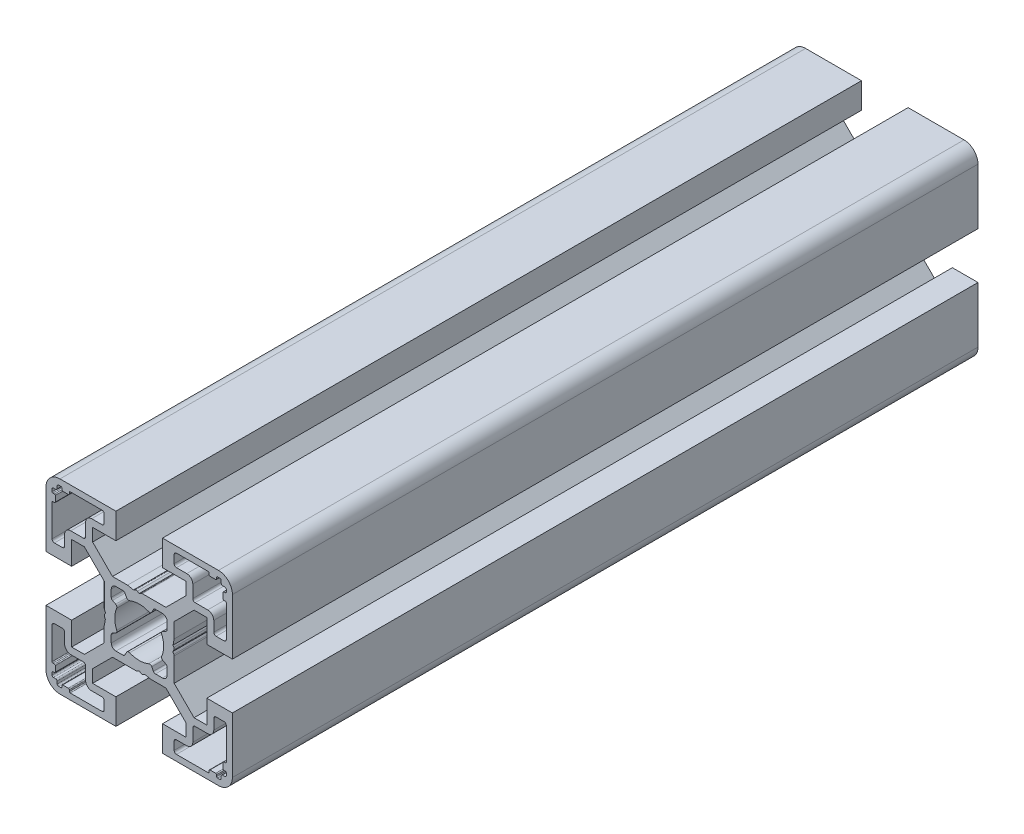
SolidWorks part; units mm, degrees
ref_plane "Front Plane" through (0, 0, 0) normal (0, 0, 1) x (1, 0, 0)
ref_plane "Top Plane" through (0, 0, 0) normal (0, 1, 0) x (1, 0, 0)
ref_plane "Right Plane" through (0, 0, 0) normal (1, 0, 0) x (0, 0, -1)
sketch "Sketch1" plane through (0, 0, 0) normal (0, 0, 1) x (1, 0, 0)
  line L0 (-11.7678, -10) -> (-14.5, -10)
  line L1 (-14.5, -10) -> (-14.5, -5)
  line L2 (-14.5, -5) -> (-20, -5)
  line L3 (-20, -5) -> (-20, -17)
  line L4 (-17, -20) -> (-5, -20)
  line L5 (-5, -20) -> (-5, -14.5)
  line L6 (-5, -14.5) -> (-10, -14.5)
  line L7 (-10, -14.5) -> (-10, -11.7678)
  line L8 (-10, -11.7678) -> (-5.7322, -7.5)
  line L9 (-5.7322, -7.5) -> (-0.6536, -7.5)
  line L10 (-0.4036, -7.433) -> (0, -7.2)
  line L11 (0, -7.2) -> (0.4036, -7.433)
  line L12 (0.9036, -7.433) -> (1.2189, -7.251)
  line L13 (1.2189, -7.251) -> (2.5, -7.5)
  line L14 (2.5, -7.5) -> (5.7322, -7.5)
  line L15 (5.7322, -7.5) -> (10, -11.7678)
  line L16 (10, -11.7678) -> (10, -14.5)
  line L17 (10, -14.5) -> (5, -14.5)
  line L18 (5, -14.5) -> (5, -20)
  line L19 (5, -20) -> (17, -20)
  line L20 (20, -17) -> (20, -5)
  line L21 (20, -5) -> (14.5, -5)
  line L22 (14.5, -5) -> (14.5, -10)
  line L23 (14.5, -10) -> (11.7678, -10)
  line L24 (11.7678, -10) -> (7.5, -5.7322)
  line L25 (7.5, -5.7322) -> (7.5, -0.6536)
  line L26 (7.433, -0.4036) -> (7.2, 0)
  line L27 (7.2, 0) -> (7.433, 0.4036)
  line L28 (7.433, 0.9036) -> (7.251, 1.2189)
  line L29 (7.251, 1.2189) -> (7.5, 2.5)
  line L30 (7.5, 2.5) -> (7.5, 5.7322)
  line L31 (7.5, 5.7322) -> (11.7678, 10)
  line L32 (11.7678, 10) -> (14.5, 10)
  line L33 (14.5, 10) -> (14.5, 5)
  line L34 (14.5, 5) -> (20, 5)
  line L35 (20, 5) -> (20, 17)
  line L36 (17, 20) -> (5, 20)
  line L37 (5, 20) -> (5, 14.5)
  line L38 (5, 14.5) -> (10, 14.5)
  line L39 (10, 14.5) -> (10, 11.7678)
  line L40 (10, 11.7678) -> (5.7322, 7.5)
  line L41 (5.7322, 7.5) -> (0.6536, 7.5)
  line L42 (0.4036, 7.433) -> (0, 7.2)
  line L43 (0, 7.2) -> (-0.4036, 7.433)
  line L44 (-0.9036, 7.433) -> (-1.2189, 7.251)
  line L45 (-1.2189, 7.251) -> (-2.5, 7.5)
  line L46 (-2.5, 7.5) -> (-5.7322, 7.5)
  line L47 (-5.7322, 7.5) -> (-10, 11.7678)
  line L48 (-10, 11.7678) -> (-10, 14.5)
  line L49 (-10, 14.5) -> (-5, 14.5)
  line L50 (-5, 14.5) -> (-5, 20)
  line L51 (-5, 20) -> (-17, 20)
  line L52 (-20, 17) -> (-20, 5)
  line L53 (-20, 5) -> (-14.5, 5)
  line L54 (-14.5, 5) -> (-14.5, 10)
  line L55 (-14.5, 10) -> (-11.7678, 10)
  line L56 (-11.7678, 10) -> (-7.5, 5.7322)
  line L57 (-7.5, 5.7322) -> (-7.5, 0.6536)
  line L58 (-7.433, 0.4036) -> (-7.2, 0)
  line L59 (-7.2, 0) -> (-7.433, -0.4036)
  line L60 (-7.433, -0.9036) -> (-7.251, -1.2189)
  line L61 (-7.251, -1.2189) -> (-7.5, -2.5)
  line L62 (-7.5, -2.5) -> (-7.5, -5.7322)
  line L63 (-7.5, -5.7322) -> (-11.7678, -10)
  line L64 (7.5, 16.5) -> (7.5, 18.2)
  line L65 (8, 18.7) -> (14.8, 18.7)
  line L66 (15, 18.5) -> (15, 18.2)
  line L67 (15.2, 18) -> (16.4, 18)
  line L68 (16.6, 18.2) -> (16.6, 18.5)
  line L69 (16.8, 18.7) -> (17.3, 18.7)
  line L70 (17.6, 18.4) -> (17.6, 17.9)
  line L71 (17.9, 17.6) -> (18.4, 17.6)
  line L72 (18.7, 17.3) -> (18.7, 16.8)
  line L73 (18.5, 16.6) -> (18.2, 16.6)
  line L74 (18, 16.4) -> (18, 15.2)
  line L75 (18.2, 15) -> (18.5, 15)
  line L76 (18.7, 14.8) -> (18.7, 8)
  line L77 (18.2, 7.5) -> (16.5, 7.5)
  line L78 (16, 8) -> (16, 10.2)
  line L79 (14.7, 11.5) -> (12, 11.5)
  line L80 (11.5, 12) -> (11.5, 14.7)
  line L81 (10.2, 16) -> (8, 16)
  line L82 (14.8, -18.7) -> (8, -18.7)
  line L83 (7.5, -18.2) -> (7.5, -16.5)
  line L84 (8, -16) -> (10.2, -16)
  line L85 (11.5, -14.7) -> (11.5, -12)
  line L86 (12, -11.5) -> (14.7, -11.5)
  line L87 (16, -10.2) -> (16, -8)
  line L88 (16.5, -7.5) -> (18.2, -7.5)
  line L89 (18.7, -8) -> (18.7, -14.8)
  line L90 (18.5, -15) -> (18.2, -15)
  line L91 (18, -15.2) -> (18, -16.4)
  line L92 (18.2, -16.6) -> (18.5, -16.6)
  line L93 (18.7, -16.8) -> (18.7, -17.3)
  line L94 (18.4, -17.6) -> (17.9, -17.6)
  line L95 (17.6, -17.9) -> (17.6, -18.4)
  line L96 (17.3, -18.7) -> (16.8, -18.7)
  line L97 (16.6, -18.5) -> (16.6, -18.2)
  line L98 (16.4, -18) -> (15.2, -18)
  line L99 (15, -18.2) -> (15, -18.5)
  line L100 (-18.7, 16.8) -> (-18.7, 17.3)
  line L101 (-18.4, 17.6) -> (-17.9, 17.6)
  line L102 (-17.6, 17.9) -> (-17.6, 18.4)
  line L103 (-17.3, 18.7) -> (-16.8, 18.7)
  line L104 (-16.6, 18.5) -> (-16.6, 18.2)
  line L105 (-16.4, 18) -> (-15.2, 18)
  line L106 (-15, 18.2) -> (-15, 18.5)
  line L107 (-14.8, 18.7) -> (-8, 18.7)
  line L108 (-7.5, 18.2) -> (-7.5, 16.5)
  line L109 (-8, 16) -> (-10.2, 16)
  line L110 (-11.5, 14.7) -> (-11.5, 12)
  line L111 (-12, 11.5) -> (-14.7, 11.5)
  line L112 (-16, 10.2) -> (-16, 8)
  line L113 (-16.5, 7.5) -> (-18.2, 7.5)
  line L114 (-18.7, 8) -> (-18.7, 14.8)
  line L115 (-18.5, 15) -> (-18.2, 15)
  line L116 (-18, 15.2) -> (-18, 16.4)
  line L117 (-18.2, 16.6) -> (-18.5, 16.6)
  line L118 (-18.7, -14.8) -> (-18.7, -8)
  line L119 (-18.2, -7.5) -> (-16.5, -7.5)
  line L120 (-16, -8) -> (-16, -10.2)
  line L121 (-14.7, -11.5) -> (-12, -11.5)
  line L122 (-11.5, -12) -> (-11.5, -14.7)
  line L123 (-10.2, -16) -> (-8, -16)
  line L124 (-7.5, -16.5) -> (-7.5, -18.2)
  line L125 (-8, -18.7) -> (-14.8, -18.7)
  line L126 (-15, -18.5) -> (-15, -18.2)
  line L127 (-15.2, -18) -> (-16.4, -18)
  line L128 (-16.6, -18.2) -> (-16.6, -18.5)
  line L129 (-16.8, -18.7) -> (-17.3, -18.7)
  line L130 (-17.6, -18.4) -> (-17.6, -17.9)
  line L131 (-17.9, -17.6) -> (-18.4, -17.6)
  line L132 (-18.7, -17.3) -> (-18.7, -16.8)
  line L133 (-18.5, -16.6) -> (-18.2, -16.6)
  line L134 (-18, -16.4) -> (-18, -15.2)
  line L135 (-18.2, -15) -> (-18.5, -15)
  line L136 (-6, 3.4907) -> (-6, 5)
  line L137 (-5, 6) -> (-3.4907, 6)
  line L138 (-3.0492, 5.7347) -> (-2.6892, 5.0577)
  line L139 (2.6892, 5.0577) -> (3.0492, 5.7347)
  line L140 (3.4907, 6) -> (5, 6)
  line L141 (6, 5) -> (6, 3.4907)
  line L142 (5.7347, 3.0492) -> (5.0577, 2.6892)
  line L143 (5.0577, -2.6892) -> (5.7347, -3.0492)
  line L144 (6, -3.4907) -> (6, -5)
  line L145 (5, -6) -> (3.4907, -6)
  line L146 (3.0492, -5.7347) -> (2.6892, -5.0577)
  line L147 (-2.6892, -5.0577) -> (-3.0492, -5.7347)
  line L148 (-3.4907, -6) -> (-5, -6)
  line L149 (-6, -5) -> (-6, -3.4907)
  line L150 (-5.7347, -3.0492) -> (-5.0577, -2.6892)
  line L151 (-5.0577, 2.6892) -> (-5.7347, 3.0492)
  arc A0 (-20, -17) -> (-17, -20) centre (-17, -17) ccw
  arc A1 (-0.6536, -7.5) -> (-0.4036, -7.433) centre (-0.6536, -7) ccw
  arc A2 (0.4036, -7.433) -> (0.9036, -7.433) centre (0.6536, -7) ccw
  arc A3 (17, -20) -> (20, -17) centre (17, -17) ccw
  arc A4 (7.5, -0.6536) -> (7.433, -0.4036) centre (7, -0.6536) ccw
  arc A5 (7.433, 0.4036) -> (7.433, 0.9036) centre (7, 0.6536) ccw
  arc A6 (20, 17) -> (17, 20) centre (17, 17) ccw
  arc A7 (0.6536, 7.5) -> (0.4036, 7.433) centre (0.6536, 7) ccw
  arc A8 (-0.4036, 7.433) -> (-0.9036, 7.433) centre (-0.6536, 7) ccw
  arc A9 (-17, 20) -> (-20, 17) centre (-17, 17) ccw
  arc A10 (-7.5, 0.6536) -> (-7.433, 0.4036) centre (-7, 0.6536) ccw
  arc A11 (-7.433, -0.4036) -> (-7.433, -0.9036) centre (-7, -0.6536) ccw
  arc A12 (8, 16) -> (7.5, 16.5) centre (8, 16.5) cw
  arc A13 (7.5, 18.2) -> (8, 18.7) centre (8, 18.2) cw
  arc A14 (14.8, 18.7) -> (15, 18.5) centre (14.8, 18.5) cw
  arc A15 (15, 18.2) -> (15.2, 18) centre (15.2, 18.2) ccw
  arc A16 (16.4, 18) -> (16.6, 18.2) centre (16.4, 18.2) ccw
  arc A17 (16.6, 18.5) -> (16.8, 18.7) centre (16.8, 18.5) cw
  arc A18 (17.3, 18.7) -> (17.6, 18.4) centre (17.3, 18.4) cw
  arc A19 (17.6, 17.9) -> (17.9, 17.6) centre (17.9, 17.9) ccw
  arc A20 (18.4, 17.6) -> (18.7, 17.3) centre (18.4, 17.3) cw
  arc A21 (18.7, 16.8) -> (18.5, 16.6) centre (18.5, 16.8) cw
  arc A22 (18.2, 16.6) -> (18, 16.4) centre (18.2, 16.4) ccw
  arc A23 (18, 15.2) -> (18.2, 15) centre (18.2, 15.2) ccw
  arc A24 (18.5, 15) -> (18.7, 14.8) centre (18.5, 14.8) cw
  arc A25 (18.7, 8) -> (18.2, 7.5) centre (18.2, 8) cw
  arc A26 (16.5, 7.5) -> (16, 8) centre (16.5, 8) cw
  arc A27 (16, 10.2) -> (14.7, 11.5) centre (14.7, 10.2) ccw
  arc A28 (12, 11.5) -> (11.5, 12) centre (12, 12) cw
  arc A29 (11.5, 14.7) -> (10.2, 16) centre (10.2, 14.7) ccw
  arc A30 (8, -18.7) -> (7.5, -18.2) centre (8, -18.2) cw
  arc A31 (7.5, -16.5) -> (8, -16) centre (8, -16.5) cw
  arc A32 (10.2, -16) -> (11.5, -14.7) centre (10.2, -14.7) ccw
  arc A33 (11.5, -12) -> (12, -11.5) centre (12, -12) cw
  arc A34 (14.7, -11.5) -> (16, -10.2) centre (14.7, -10.2) ccw
  arc A35 (16, -8) -> (16.5, -7.5) centre (16.5, -8) cw
  arc A36 (18.2, -7.5) -> (18.7, -8) centre (18.2, -8) cw
  arc A37 (18.7, -14.8) -> (18.5, -15) centre (18.5, -14.8) cw
  arc A38 (18.2, -15) -> (18, -15.2) centre (18.2, -15.2) ccw
  arc A39 (18, -16.4) -> (18.2, -16.6) centre (18.2, -16.4) ccw
  arc A40 (18.5, -16.6) -> (18.7, -16.8) centre (18.5, -16.8) cw
  arc A41 (18.7, -17.3) -> (18.4, -17.6) centre (18.4, -17.3) cw
  arc A42 (17.9, -17.6) -> (17.6, -17.9) centre (17.9, -17.9) ccw
  arc A43 (17.6, -18.4) -> (17.3, -18.7) centre (17.3, -18.4) cw
  arc A44 (16.8, -18.7) -> (16.6, -18.5) centre (16.8, -18.5) cw
  arc A45 (16.6, -18.2) -> (16.4, -18) centre (16.4, -18.2) ccw
  arc A46 (15.2, -18) -> (15, -18.2) centre (15.2, -18.2) ccw
  arc A47 (15, -18.5) -> (14.8, -18.7) centre (14.8, -18.5) cw
  arc A48 (-18.5, 16.6) -> (-18.7, 16.8) centre (-18.5, 16.8) cw
  arc A49 (-18.7, 17.3) -> (-18.4, 17.6) centre (-18.4, 17.3) cw
  arc A50 (-17.9, 17.6) -> (-17.6, 17.9) centre (-17.9, 17.9) ccw
  arc A51 (-17.6, 18.4) -> (-17.3, 18.7) centre (-17.3, 18.4) cw
  arc A52 (-16.8, 18.7) -> (-16.6, 18.5) centre (-16.8, 18.5) cw
  arc A53 (-16.6, 18.2) -> (-16.4, 18) centre (-16.4, 18.2) ccw
  arc A54 (-15.2, 18) -> (-15, 18.2) centre (-15.2, 18.2) ccw
  arc A55 (-15, 18.5) -> (-14.8, 18.7) centre (-14.8, 18.5) cw
  arc A56 (-8, 18.7) -> (-7.5, 18.2) centre (-8, 18.2) cw
  arc A57 (-7.5, 16.5) -> (-8, 16) centre (-8, 16.5) cw
  arc A58 (-10.2, 16) -> (-11.5, 14.7) centre (-10.2, 14.7) ccw
  arc A59 (-11.5, 12) -> (-12, 11.5) centre (-12, 12) cw
  arc A60 (-14.7, 11.5) -> (-16, 10.2) centre (-14.7, 10.2) ccw
  arc A61 (-16, 8) -> (-16.5, 7.5) centre (-16.5, 8) cw
  arc A62 (-18.2, 7.5) -> (-18.7, 8) centre (-18.2, 8) cw
  arc A63 (-18.7, 14.8) -> (-18.5, 15) centre (-18.5, 14.8) cw
  arc A64 (-18.2, 15) -> (-18, 15.2) centre (-18.2, 15.2) ccw
  arc A65 (-18, 16.4) -> (-18.2, 16.6) centre (-18.2, 16.4) ccw
  arc A66 (-18.5, -15) -> (-18.7, -14.8) centre (-18.5, -14.8) cw
  arc A67 (-18.7, -8) -> (-18.2, -7.5) centre (-18.2, -8) cw
  arc A68 (-16.5, -7.5) -> (-16, -8) centre (-16.5, -8) cw
  arc A69 (-16, -10.2) -> (-14.7, -11.5) centre (-14.7, -10.2) ccw
  arc A70 (-12, -11.5) -> (-11.5, -12) centre (-12, -12) cw
  arc A71 (-11.5, -14.7) -> (-10.2, -16) centre (-10.2, -14.7) ccw
  arc A72 (-8, -16) -> (-7.5, -16.5) centre (-8, -16.5) cw
  arc A73 (-7.5, -18.2) -> (-8, -18.7) centre (-8, -18.2) cw
  arc A74 (-14.8, -18.7) -> (-15, -18.5) centre (-14.8, -18.5) cw
  arc A75 (-15, -18.2) -> (-15.2, -18) centre (-15.2, -18.2) ccw
  arc A76 (-16.4, -18) -> (-16.6, -18.2) centre (-16.4, -18.2) ccw
  arc A77 (-16.6, -18.5) -> (-16.8, -18.7) centre (-16.8, -18.5) cw
  arc A78 (-17.3, -18.7) -> (-17.6, -18.4) centre (-17.3, -18.4) cw
  arc A79 (-17.6, -17.9) -> (-17.9, -17.6) centre (-17.9, -17.9) ccw
  arc A80 (-18.4, -17.6) -> (-18.7, -17.3) centre (-18.4, -17.3) cw
  arc A81 (-18.7, -16.8) -> (-18.5, -16.6) centre (-18.5, -16.8) cw
  arc A82 (-18.2, -16.6) -> (-18, -16.4) centre (-18.2, -16.4) ccw
  arc A83 (-18, -15.2) -> (-18.2, -15) centre (-18.2, -15.2) ccw
  arc A84 (-5.7347, 3.0492) -> (-6, 3.4907) centre (-5.5, 3.4907) cw
  arc A85 (-6, 5) -> (-5, 6) centre (-5, 5) cw
  arc A86 (-3.4907, 6) -> (-3.0492, 5.7347) centre (-3.4907, 5.5) cw
  arc A87 (-2.6892, 5.0577) -> (-2.0523, 4.8322) centre (-2.2478, 5.2925) ccw
  arc A88 (-2.0523, 4.8322) -> (2.0523, 4.8322) centre (0, 0) cw
  arc A89 (2.0523, 4.8322) -> (2.6892, 5.0577) centre (2.2478, 5.2925) ccw
  arc A90 (3.0492, 5.7347) -> (3.4907, 6) centre (3.4907, 5.5) cw
  arc A91 (5, 6) -> (6, 5) centre (5, 5) cw
  arc A92 (6, 3.4907) -> (5.7347, 3.0492) centre (5.5, 3.4907) cw
  arc A93 (5.0577, 2.6892) -> (4.8322, 2.0523) centre (5.2925, 2.2478) ccw
  arc A94 (4.8322, 2.0523) -> (4.8322, -2.0523) centre (0, 0) cw
  arc A95 (4.8322, -2.0523) -> (5.0577, -2.6892) centre (5.2925, -2.2478) ccw
  arc A96 (5.7347, -3.0492) -> (6, -3.4907) centre (5.5, -3.4907) cw
  arc A97 (6, -5) -> (5, -6) centre (5, -5) cw
  arc A98 (3.4907, -6) -> (3.0492, -5.7347) centre (3.4907, -5.5) cw
  arc A99 (2.6892, -5.0577) -> (2.0523, -4.8322) centre (2.2478, -5.2925) ccw
  arc A100 (2.0523, -4.8322) -> (-2.0523, -4.8322) centre (0, 0) cw
  arc A101 (-2.0523, -4.8322) -> (-2.6892, -5.0577) centre (-2.2478, -5.2925) ccw
  arc A102 (-3.0492, -5.7347) -> (-3.4907, -6) centre (-3.4907, -5.5) cw
  arc A103 (-5, -6) -> (-6, -5) centre (-5, -5) cw
  arc A104 (-6, -3.4907) -> (-5.7347, -3.0492) centre (-5.5, -3.4907) cw
  arc A105 (-5.0577, -2.6892) -> (-4.8322, -2.0523) centre (-5.2925, -2.2478) ccw
  arc A106 (-4.8322, -2.0523) -> (-4.8322, 2.0523) centre (0, 0) cw
  arc A107 (-4.8322, 2.0523) -> (-5.0577, 2.6892) centre (-5.2925, 2.2478) ccw
extrude "Boss-Extrude1" add sketch "Sketch1" against normal blind 160
